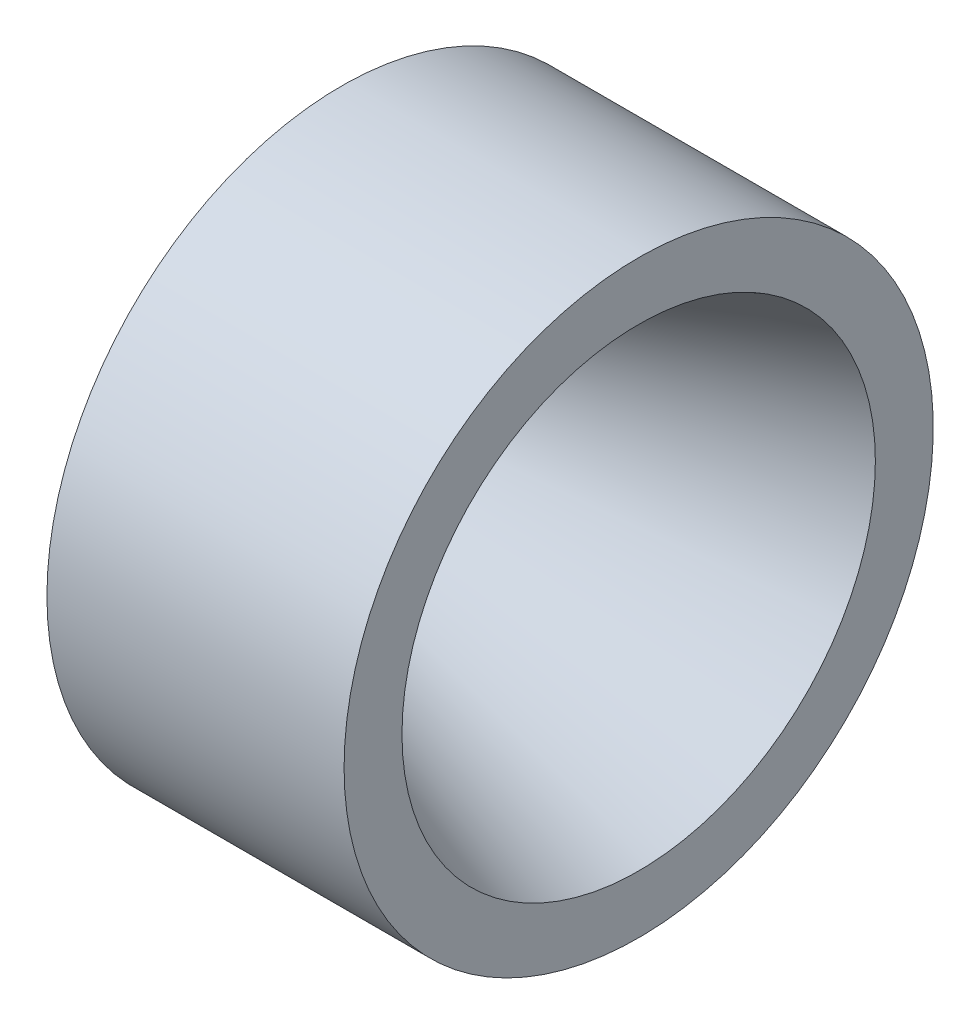
SolidWorks part; units mm, degrees
material "1023 Carbon Steel Sheet (SS)"
ref_plane "Front Plane" through (0, 0, 0) normal (0, 0, 1) x (1, 0, 0)
ref_plane "Top Plane" through (0, 0, 0) normal (0, 1, 0) x (1, 0, 0)
ref_plane "Right Plane" through (0, 0, 0) normal (1, 0, 0) x (0, 0, -1)
sketch "Sketch1" plane through (0, 0, 0) normal (0, 0, 1) x (1, 0, 0)
  line L0 (0, 0) -> (280.924, 0) construction
  line L1 (280.924, 0) -> (280.911, 30.48) construction
  line L3 (280.911, 30.48) -> (351.3696, 56.1248)
  line L4 (280.924, 0) -> (534.924, 0) construction
  line L5 (351.3696, 56.1248) -> (351.3696, 69.85)
  line L6 (280.911, 30.48) -> (280.911, 50.8)
  line L8 (280.911, 50.8) -> (280.911, 69.85)
  line L9 (280.911, 69.85) -> (351.3696, 69.85)
  dimension "D1" = 280.924
  dimension "D2" = 30.48
  dimension "D3" = 254
  dimension "D4" = 20
  dimension "D5" = 56.1248
  dimension "D6" = 139.7
  dimension "D7" = 20.32
revolve "Revolve1" add sketch "Sketch1" angle 360 about L0
sketch "Sketch2" plane through (0, 0, 0) normal (0, 0, 1) x (1, 0, 0)
  line L0 (280.911, 30.48) -> (280.911, -30.48) construction
  point P0 (280.911, 0)
sketch "Sketch4" plane through (280.911, 0, 0) normal (-1, 0, 0) x (0, 0, 1)
  line L0 (0, 0) -> (0, 59.69)
  circle A0 centre (0, 59.69) radius 2.54
  dimension "D2" = 5.08
  dimension "D1" = 59.69
extrude "Cut-Extrude1" cut sketch "Sketch4" against normal blind 30.48
pattern_circular "CirPattern1" count 12 over 360 about axis through (0, 0, 0) along (1, 0, 0) of "Cut-Extrude1"
